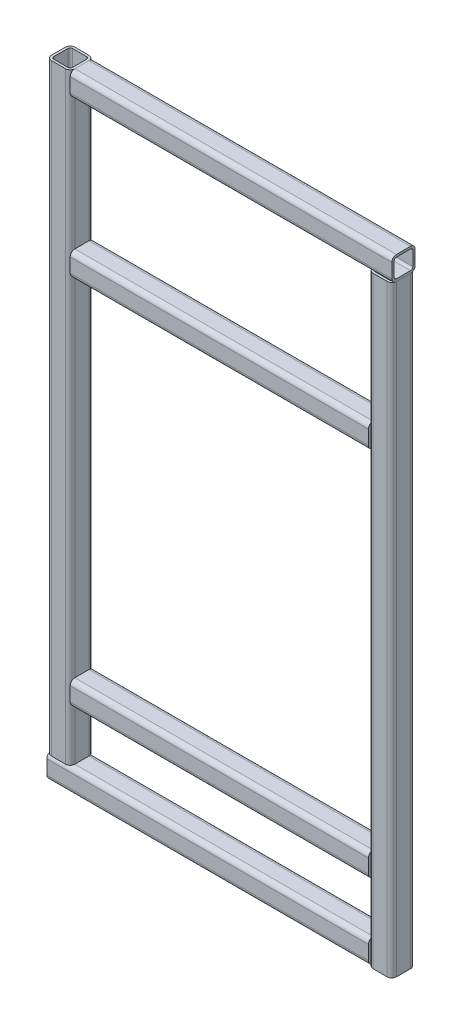
SolidWorks part; units mm, degrees
material "6061-T4 (SS)"
ref_plane "Front Plane" through (0, 0, 0) normal (0, 0, 1) x (1, 0, 0)
ref_plane "Top Plane" through (0, 0, 0) normal (0, 1, 0) x (1, 0, 0)
ref_plane "Right Plane" through (0, 0, 0) normal (1, 0, 0) x (0, 0, -1)
sketch "Sketch1" plane through (0, 0, 0) normal (0, 0, 1) x (1, 0, 0)
  line L0 (137.5, 124.05) -> (-137.5, 124.05)
  line L1 (-137.5, -257.5) -> (137.5, -257.5)
  line L2 (-137.5, -257.5) -> (-137.5, 257.5)
  line L3 (-137.5, 257.5) -> (137.5, 257.5)
  line L4 (137.5, -257.5) -> (137.5, 257.5)
  line L5 (-137.5, -257.5) -> (137.5, 257.5) construction
  line L6 (-137.5, 257.5) -> (137.5, -257.5) construction
  line L7 (-137.5, -193.48) -> (137.5, -193.48)
  point P0 (0, 0)
  dimension "D1" = 275
  dimension "D2" = 515
  dimension "D3" = 381.55
  dimension "D4" = 64.02
other "Square tube 20 X 20 X 2(1)"
ref_plane "Plane1" through (-137.5, 257.5, 0) normal (1, 0, 0) x (0, 1, 0)
sketch "Sketch16" plane through (-137.5, 257.5, 0) normal (1, 0, 0) x (0, 1, 0)
  line L0 (-6, -8) -> (6, -8)
  line L1 (-8, -6) -> (-8, 6)
  line L2 (6, 8) -> (-6, 8)
  line L3 (8, 6) -> (8, -6)
  line L4 (-6, -10) -> (6, -10)
  line L5 (-10, -6) -> (-10, 6)
  line L6 (6, 10) -> (-6, 10)
  line L7 (10, 6) -> (10, -6)
  arc A0 (10, 6) -> (6, 10) centre (6, 6) ccw
  arc A1 (6, -10) -> (10, -6) centre (6, -6) ccw
  arc A2 (-10, -6) -> (-6, -10) centre (-6, -6) ccw
  arc A3 (-6, 10) -> (-10, 6) centre (-6, 6) ccw
  arc A4 (-6, 8) -> (-8, 6) centre (-6, 6) ccw
  arc A5 (8, 6) -> (6, 8) centre (6, 6) ccw
  arc A6 (6, -8) -> (8, -6) centre (6, -6) ccw
  arc A7 (-8, -6) -> (-6, -8) centre (-6, -6) ccw
  point P0 (-10, 0)
  point P1 (10, 0)
  point P2 (0, 10)
  point P3 (0, -10)
  point P4 (0, 0)
  point P5 (-10, -10)
  point P6 (10, -10)
  point P7 (10, 10)
  point P8 (-10, 10)
  point P33 (0, 0)
  dimension "D1" = 4
  dimension "Thickness" = 2
  dimension "V_leg" = 20
sketch "Sketch17" plane through (0, 0, -10) normal (0, 0, -1) x (-1, 0, 0)
  line L0 (0, 0) -> (0, -257.5) construction
  line L1 (137.5, -257.5) -> (-137.5, -257.5) construction
  line L2 (0, -257.5) -> (35.5, -257.5) construction
  circle A0 centre (35.5, -257.5) radius 2.5
  circle A1 centre (-35.5, -257.5) radius 2.5
  dimension "D2" = 5
  dimension "D1" = 35.5
extrude "Cut-Extrude1" cut sketch "Sketch17" against normal blind 5
